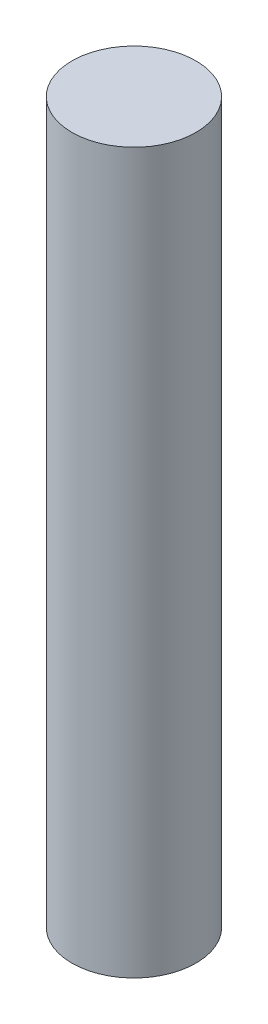
SolidWorks part; units mm, degrees
ref_plane "Front Plane" through (0, 0, 0) normal (0, 0, 1) x (1, 0, 0)
ref_plane "Top Plane" through (0, 0, 0) normal (0, 1, 0) x (1, 0, 0)
ref_plane "Right Plane" through (0, 0, 0) normal (1, 0, 0) x (0, 0, -1)
sketch "Sketch1" plane through (0, 0, 0) normal (0, 1, 0) x (1, 0, 0)
  circle A0 centre (0, 0) radius 5
  dimension "D1" = 10
extrude "Boss-Extrude1" add sketch "Sketch1" along normal blind 58
